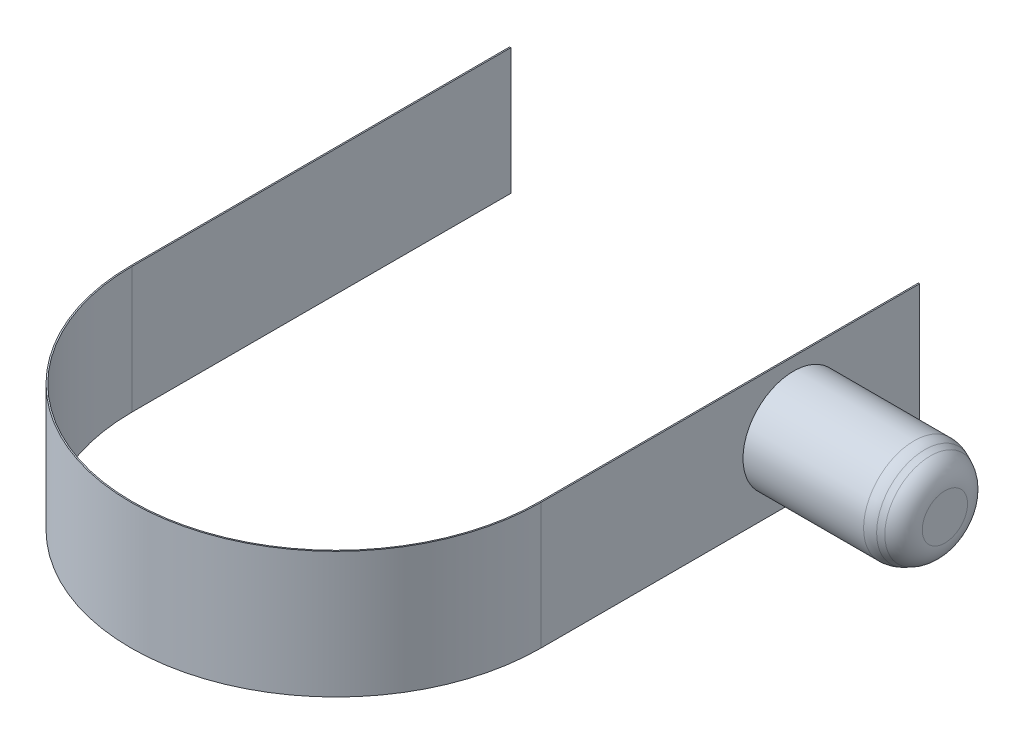
SolidWorks part; units mm, degrees
ref_plane "Front Plane" through (0, 0, 0) normal (0, 0, 1) x (1, 0, 0)
ref_plane "Top Plane" through (0, 0, 0) normal (0, 1, 0) x (1, 0, 0)
ref_plane "Right Plane" through (0, 0, 0) normal (1, 0, 0) x (0, 0, -1)
sketch "Sketch4" plane through (0, 0, 0) normal (0, 0, 1) x (1, 0, 0)
  line L0 (-16.2481, 5) -> (-16.2481, -5) construction
  line L1 (16.2481, 5) -> (16.2481, -5) construction
  circle A0 centre (0, 0) radius 17 construction
  dimension "D1" = 34
  dimension "D2" = 10
sketch "Sketch3" plane through (0, 0, 0) normal (0, 1, 0) x (1, 0, 0)
  line L0 (-16.2481, 0) -> (-16.2481, 30)
  line L1 (16.2481, 0) -> (16.2481, 30)
  arc A0 (-16.2481, 0) -> (16.2481, 0) centre (0, 0) ccw
  point P1 (0, 0)
  point P3 (16.2481, 30.086)
  point P13 (-16.2481, 0)
  dimension "D1" = 30
extrude "Extrude-Thin1" add sketch "Sketch3" along normal mid plane 10 thin contours L0 A0 L1
sketch "Sketch5" plane through (-16.2481, 0, 0) normal (-1, 0, 0) x (0, 0, 1)
  line L0 (0, 5) -> (0, -5)
  line L1 (0, 5) -> (-26.3898, 5)
  line L2 (0, -5) -> (-26.3898, -5)
  line L3 (-26.3898, 5) -> (-26.3898, -5)
extrude "Boss-Extrude1" add sketch "Sketch5" against normal up to surface (0.1 mm away) up to face at (-16.1481, 0, -15)
sketch "Sketch6" plane through (16.2481, 0, 0) normal (1, 0, 0) x (0, 0, -1)
  line L2 (0, 5) -> (0, -5) construction
  line L3 (0, -5) -> (30, -5) construction
  circle A0 centre (20, 0) radius 4
  point P6 (0, 0)
  dimension "D1" = 8
  dimension "D3" = 5
  dimension "D2" = 20
extrude "Boss-Extrude2" add sketch "Sketch6" along normal blind 12
chamfer "Chamfer1" distance 2 angle 25 1 edges at (28.2481, 0, -24)
fillet "Fillet1" radius 2 2 edges at (28.2481, 0, -23.0674) (26.2481, 0, -24)
